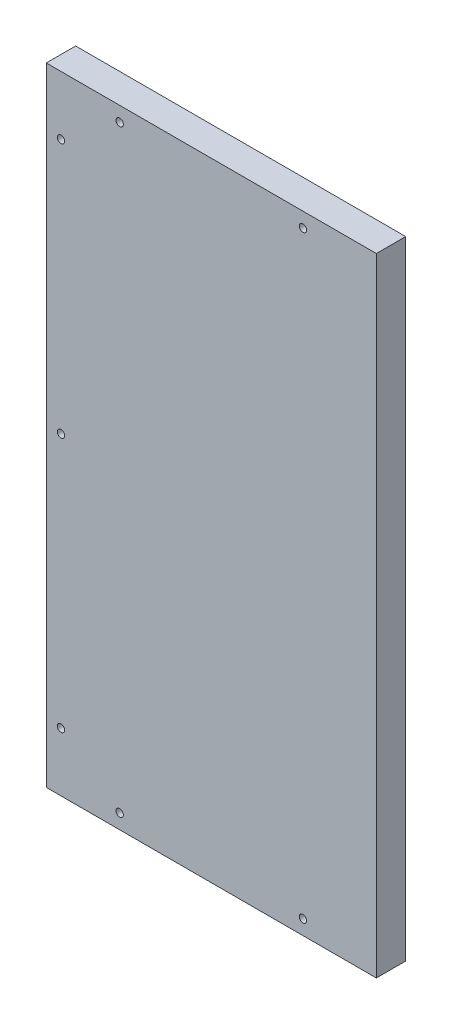
SolidWorks part; units mm, degrees
material "Beech"
ref_plane "Front Plane" through (0, 0, 0) normal (0, 0, 1) x (1, 0, 0)
ref_plane "Top Plane" through (0, 0, 0) normal (0, 1, 0) x (1, 0, 0)
ref_plane "Right Plane" through (0, 0, 0) normal (1, 0, 0) x (0, 0, -1)
sketch "Sketch1" plane through (0, 0, 0) normal (0, 0, 1) x (1, 0, 0)
  line L0 (-234.753, 19.05) -> (-234.753, 0) construction
  line L1 (-234.753, 82.8417) -> (-91.9973, 82.8417)
  line L2 (-234.753, 82.8417) -> (-234.753, -188.5238)
  line L3 (-234.753, -188.5238) -> (-91.9973, -188.5238)
  line L4 (-91.9973, 82.8417) -> (-91.9973, -188.5238)
extrude "Boss-Extrude1" add sketch "Sketch1" along normal blind 12.7
hole_wizard "Hole1" positions "Sketch2" profile "Sketch3" legacy
sketch "Sketch2" plane through (181.0394, -52.975, 0) normal (0, 0, -1) x (0, -1, 0)
  line L0 (-129.4667, 415.7924) -> (-129.4667, 273.0368) construction
  line L5 (-135.8167, 409.4424) -> (135.5488, 409.4424) construction
  line L10 (-135.8167, 279.3868) -> (135.5488, 279.3868) construction
  line L11 (-0.134, 409.4424) -> (-0.134, 279.3868) construction
  point P22 (-129.4667, 384.0424)
  point P24 (-129.4667, 304.7868)
  point P26 (-110.4167, 409.4424)
  point P30 (-0.134, 409.4424)
  point P50 (110.1488, 409.4424)
  point P51 (129.1988, 304.7868)
  point P52 (129.1988, 384.0424)
sketch "Sketch3" plane through (-203.003, -182.1738, 0) normal (1, 0, 0) x (0, 1, 0)
  line L0 (0, 0) -> (0, 32.7039)
  line L1 (0, 32.7039) -> (1.5875, 31.75)
  line L2 (1.5875, 31.75) -> (1.5875, 4.0177)
  line L3 (1.5875, 4.0177) -> (5.08, 0)
  line L4 (5.08, 0) -> (0, 0)
  line L5 (0, -14.3089) -> (0, 102.4216) construction
  line L6 (0, 32.7039) -> (-1.5875, 31.75) construction
  line L7 (-1.5875, 4.0177) -> (-5.08, 0) construction
  dimension "Diameter" = 3.175
  dimension "Depth" = 31.75
  dimension "C-Sink Diameter" = 10.16
  dimension "C-Sink Angle" = 82
  dimension "Drill Angle" = 118
chamfer "Chamfer1" [suppressed] distance 3.175 angle 45
